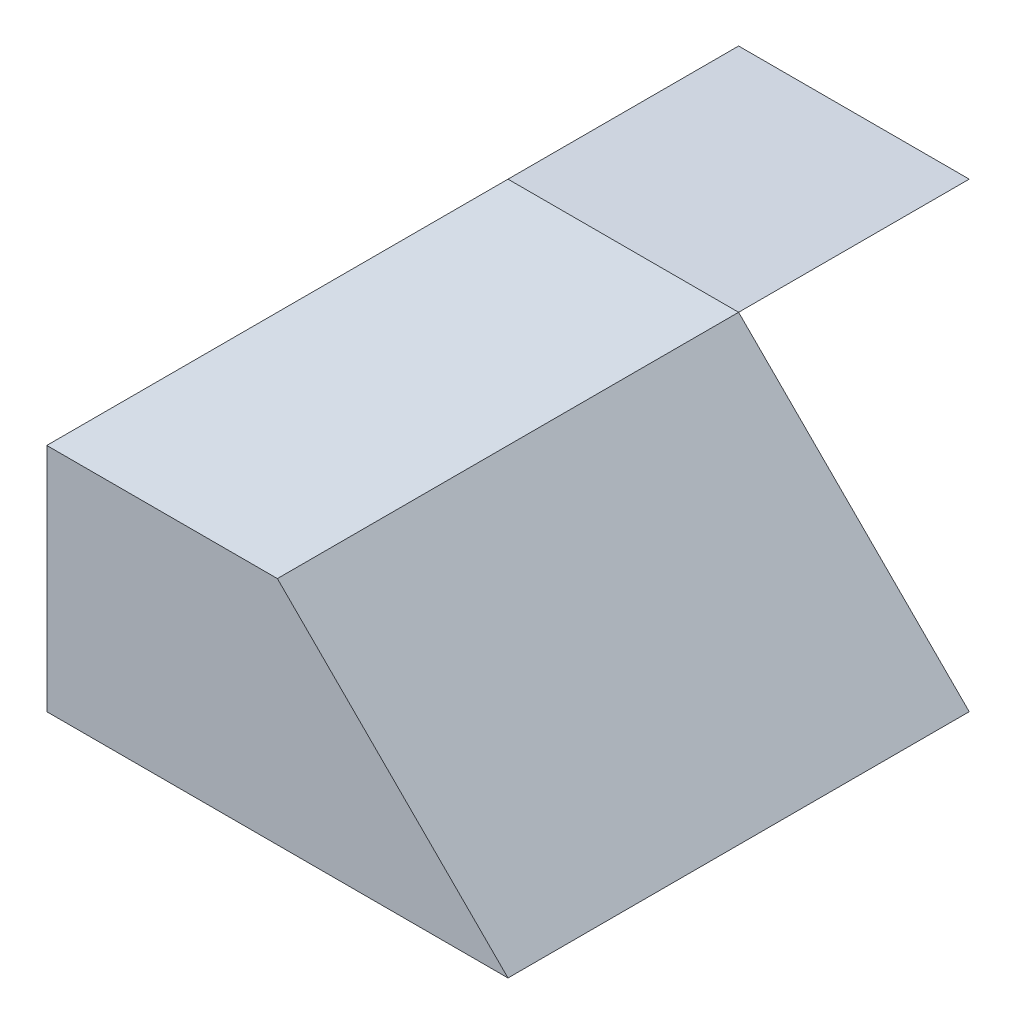
SolidWorks part; units mm, degrees
ref_plane "Front" through (0, 0, 0) normal (0, 0, 1) x (1, 0, 0)
ref_plane "Top" through (0, 0, 0) normal (0, 1, 0) x (1, 0, 0)
ref_plane "Right" through (0, 0, 0) normal (1, 0, 0) x (0, 0, -1)
sketch "Sketch1" plane through (0, 0, 0) normal (0, 1, 0) x (1, 0, 0)
  line L1 (-2, -2) -> (2, -2)
  line L2 (-2, -2) -> (-2, 2)
  line L3 (-2, 2) -> (2, 2)
  line L4 (2, -2) -> (2, 2)
  line L5 (-2, -2) -> (2, 2) construction
  line L6 (-2, 2) -> (2, -2) construction
  point P0 (0, 0)
  dimension "D1" = 4
  dimension "D2" = 4
extrude "Boss-Extrude1" add sketch "Sketch1" along normal blind 4
sketch "Sketch2" plane through (-2, 0, 0) normal (-1, 0, 0) x (0, 0, 1)
  line L0 (0, 4) -> (2, 2)
  line L1 (-2, 4) -> (2, 4) construction
  line L2 (2, 4) -> (2, 0) construction
  line L3 (2, 2) -> (2, 4)
  line L4 (2, 4) -> (0, 4)
extrude "Cut-Extrude1" cut sketch "Sketch2" against normal blind 4
sketch "Sketch3" plane through (0, 0, 2) normal (0, 0, 1) x (1, 0, 0)
  line L0 (0, 4) -> (-2, 2)
  line L1 (2, 4) -> (-2, 4) construction
  line L2 (-2, 2) -> (-2, 4)
  line L3 (-2, 4) -> (0, 4)
  line L4 (2, 4) -> (0, 2)
  line L5 (2, 2) -> (-2, 2) construction
  line L6 (0, 2) -> (2, 0)
  line L7 (2, 0) -> (2, 4)
  line M4 (2, 0) -> (2, 2)
  line M5 (2, 2) -> (-2, 2)
extrude "Cut-Extrude2" cut sketch "Sketch3" against normal blind 4 contours L3 L2 L0 | L7 L4 M5 | L6 M5 M4
